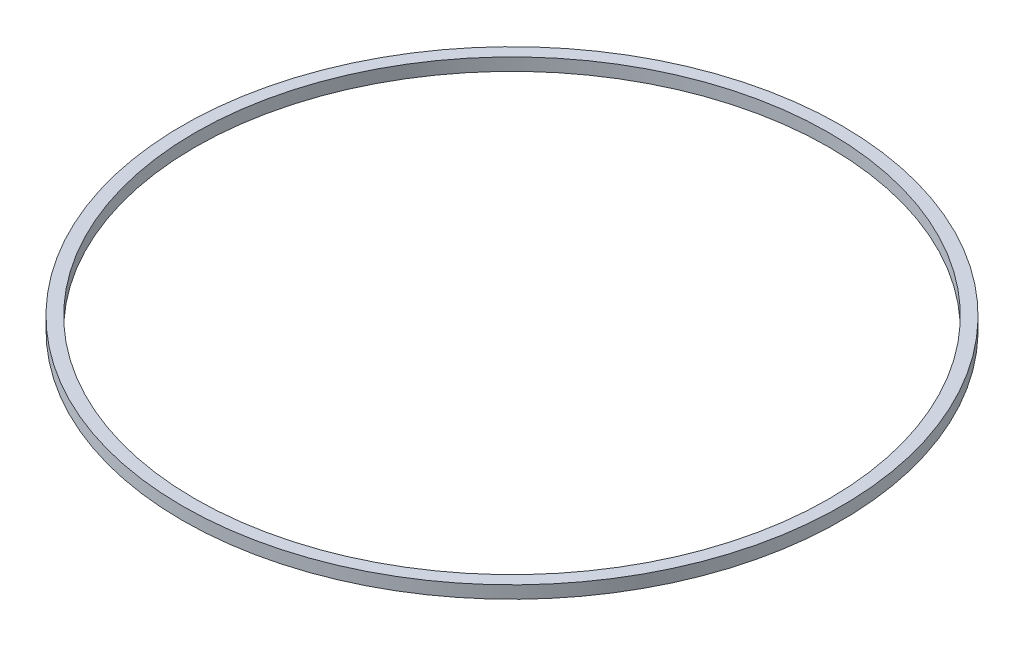
SolidWorks part; units mm, degrees
ref_plane "Front Plane" through (0, 0, 0) normal (0, 0, 1) x (1, 0, 0)
ref_plane "Top Plane" through (0, 0, 0) normal (0, 1, 0) x (1, 0, 0)
ref_plane "Right Plane" through (0, 0, 0) normal (1, 0, 0) x (0, 0, -1)
sketch "Sketch1" plane through (0, 0, 0) normal (0, 1, 0) x (1, 0, 0)
  circle A2 centre (0, 0) radius 79
  circle A3 centre (0, 0) radius 76
  dimension "D1" = 158
  dimension "D2" = 152
extrude "Boss-Extrude1" add sketch "Sketch1" along normal blind 3
